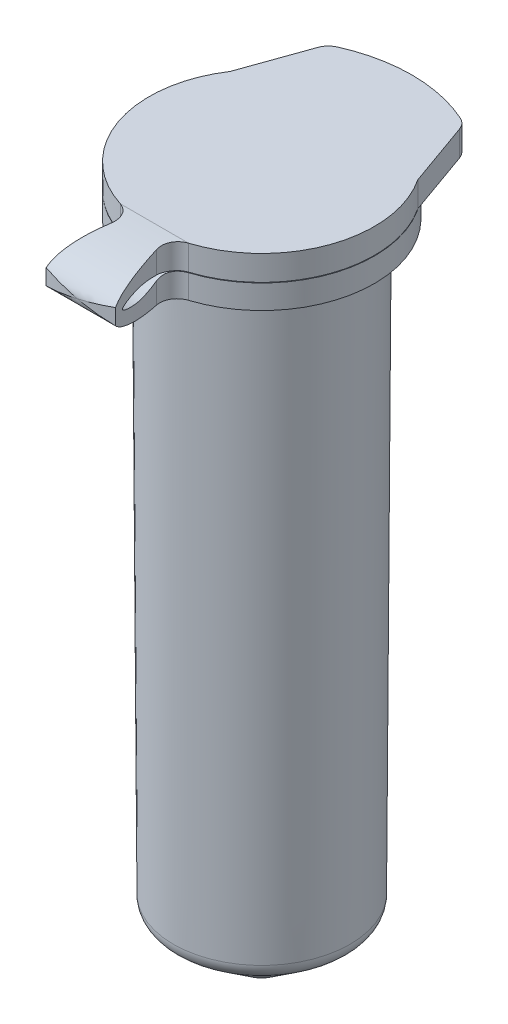
SolidWorks part; units mm, degrees
ref_plane "Front Plane" through (0, 0, 0) normal (0, 0, 1) x (1, 0, 0)
ref_plane "Top Plane" through (0, 0, 0) normal (0, 1, 0) x (1, 0, 0)
ref_plane "Right Plane" through (0, 0, 0) normal (1, 0, 0) x (0, 0, -1)
sketch "Sketch1" plane through (0, 0, 0) normal (0, 0, 1) x (1, 0, 0)
  line L0 (0, 0) -> (0, 36.0603) construction
  line L1 (1.1922, -3.4621) -> (4.774, -0.8029)
  line L2 (5.1779, -0.0058) -> (5.375, 34.2437)
  line L3 (4.1779, 0) -> (4.3787, 34.8937)
  line L4 (0.5961, -2.6592) -> (4.1779, 0)
  line L5 (5.1287, 35.6437) -> (6.6, 35.6437)
  line L6 (6.6, 35.6437) -> (6.6, 34.2437)
  line L7 (6.6, 34.2437) -> (5.375, 34.2437)
  line L8 (5.1779, -0.0058) -> (5.406, 39.6217) construction
  line L9 (4.1779, 0) -> (4.406, 39.6274) construction
  line L10 (4.3787, 34.8937) -> (5.1287, 35.6437)
  line L11 (0, -3.8563) -> (0, -2.8563)
  line L12 (4.25, 32.8937) -> (4.25, 36.3937)
  line L13 (4.25, 36.3937) -> (6, 36.3937)
  line L14 (6.6, 36.1404) -> (6.6, 37.1437)
  line L15 (6.6, 37.1437) -> (0, 37.1437)
  line L16 (0, 37.1437) -> (0, 36.3937)
  line L17 (0, 36.3937) -> (3.65, 36.3937)
  line L18 (3.65, 36.3937) -> (3.65, 32.8937)
  line L19 (3.65, 32.8937) -> (4.25, 32.8937)
  line L20 (6.6, 36.1404) -> (6.6, 35.6737)
  line L21 (6.6, 35.6737) -> (6, 35.6737)
  line L22 (6, 35.6737) -> (6, 36.3937)
  arc A0 (1.1922, -3.4621) -> (0, -3.8563) centre (0, -1.8563) cw
  arc A1 (4.774, -0.8029) -> (5.1779, -0.0058) centre (4.1779, 0) ccw
  arc A2 (4.1779, 0) -> (4.1779, 0) centre (4.1779, 0) ccw
  arc A3 (0.5961, -2.6592) -> (0, -2.8563) centre (0, -1.8563) cw
  point P9 (0, -2.3188)
  point P10 (0.6278, -3.7552)
  point P13 (5.175, -0.5052)
  dimension "D3" = 2
  dimension "D5" = 1
  dimension "D1" = 5.175
  dimension "D2" = 1.4
  dimension "D4" = 3.25
  dimension "D7" = 5.375
  dimension "D8" = 39.5
  dimension "D10" = 135
  dimension "D11" = 0.75
  dimension "D12" = 4.25
  dimension "D13" = 41
  dimension "D14" = 1.47
  dimension "D15" = 6.6
  dimension "D16" = 0.6
  dimension "D17" = 3.5
  dimension "D18" = 0.72
  dimension "D19" = 0.6
  dimension "D6" = 1
revolve "Revolve1" add sketch "Sketch1" angle 360 about L0
sketch "Sketch2" plane through (0, 37.1437, 0) normal (0, 1, 0) x (1, 0, 0)
  line L0 (-5.5, 3.6483) -> (-4.148, 7.4461)
  line L1 (0, -55) -> (0, 55) construction
  line L2 (5.5, 3.6483) -> (4.148, 7.4461)
  circle A0 centre (0, 0) radius 6.6 construction
  arc A1 (5.5, 3.6483) -> (-5.5, 3.6483) centre (0, 0) ccw
  arc A2 (3.6169, 8.0223) -> (-3.6169, 8.0223) centre (0, 0) ccw
  arc A3 (4.148, 7.4461) -> (3.6169, 8.0223) centre (3.2059, 7.1107) ccw
  arc A4 (-4.148, 7.4461) -> (-3.6169, 8.0223) centre (-3.2059, 7.1107) cw
  point P10 (0, -8.8)
  point P11 (0, 8.8)
  point P12 (0, -6.6)
  point P13 (4.0102, 7.8332)
  point P16 (-4.0102, 7.8332)
  dimension "D4" = 1
  dimension "D1" = 11
  dimension "D2" = 8.0203
  dimension "D3" = 15.4
extrude "Boss-Extrude1" add sketch "Sketch2" against normal up to surface (1.47 mm away) up to face at (0, 35.6737, -6.6)
sketch "Sketch3" plane through (0, 37.1437, 0) normal (0, 1, 0) x (1, 0, 0)
  line L1 (2.03, -10.6075) -> (3.0596, -15.9873) construction
  line L2 (0, -10.8) -> (0, -6.6)
  arc A0 (-5.5, 3.6483) -> (5.5, 3.6483) centre (0, 0) ccw construction
  arc A1 (-2.0009, -6.2894) -> (2.0009, -6.2894) centre (0, 0) ccw
  arc A2 (2.0009, -6.2894) -> (1.335, -7.4893) centre (2.304, -7.2423) ccw
  arc A3 (-2.03, -10.6075) -> (2.03, -10.6075) centre (0, 0) ccw
  arc A4 (2.03, -10.6075) -> (1.335, -7.4893) centre (-49.9111, -20.5477) ccw
  arc A5 (3.6169, 8.0223) -> (-3.6169, 8.0223) centre (0, 0) ccw construction
  arc A6 (-2.03, -10.6075) -> (-1.335, -7.4893) centre (49.9111, -20.5477) cw
  arc A7 (-2.0009, -6.2894) -> (-1.335, -7.4893) centre (-2.304, -7.2423) cw
  point P11 (0, 8.8)
  arc M7 (-5.5, 3.6483) -> (5.5, 3.6483) centre (0, 0) ccw
  dimension "D1" = 2
  dimension "D2" = 1.335
  dimension "D3" = 2.03
  dimension "D4" = 19.6
extrude "Boss-Extrude2" add sketch "Sketch3" against normal up to surface (2.9 mm away) contours A3 A4 A2 L2 M7 | A7 A6 A3 L2 M7 up to face at (0, 34.2437, -6.6)
sketch "Sketch5" plane through (0, 0, 0) normal (1, 0, 0) x (0, 0, -1)
  line L0 (-6.2894, 35.6437) -> (-6.6, 35.6437) construction
  line L1 (-6.6, 35.6737) -> (-6.2894, 35.6737) construction
  line L2 (-6.2894, 35.6437) -> (-6.6, 35.6437)
  line L3 (-6.6, 35.6737) -> (-6.2894, 35.6737)
  line L4 (-6.2894, 35.6737) -> (-6.2894, 35.6437)
  line L5 (-6.2894, 34.2437) -> (6.6, 34.2437) construction
  line L8 (3.6483, 37.1437) -> (-6.2894, 37.1437) construction
  line L9 (-6.2894, 34.2437) -> (-6.2894, 33.5334)
  line L10 (-6.2894, 33.5334) -> (-11.4674, 33.8255)
  line L11 (-11.4674, 33.8255) -> (-11.3579, 38.5445)
  line L12 (-11.3579, 38.5445) -> (-6.2894, 38.0355)
  line L13 (-6.2894, 38.0355) -> (-6.2894, 37.1437)
  spline S0 degree 3 poles (-6.6, 35.6737) (-7.519, 35.6737) (-8.4218, 36.3271) (-10.3699, 35.6587) (-8.4216, 34.9903) (-7.5213, 35.6437) (-6.6, 35.6437) knots 0 0 0 0 0.417766 0.5 0.582234 1 1 1 1
  spline S1 degree 3 poles (-6.2894, 37.1437) (-9.4319, 37.1437) (-12.1354, 35.4791) (-9.4967, 34.2437) (-6.2894, 34.2437) knots 0 0 0 0 0.503822 1 1 1 1
  point P5 (-6.2894, 35.6587)
  dimension "D1" = 0.25
  dimension "D2" = 0.25
extrude "Cut-Extrude1" cut sketch "Sketch5" against normal through all and the other way through all
